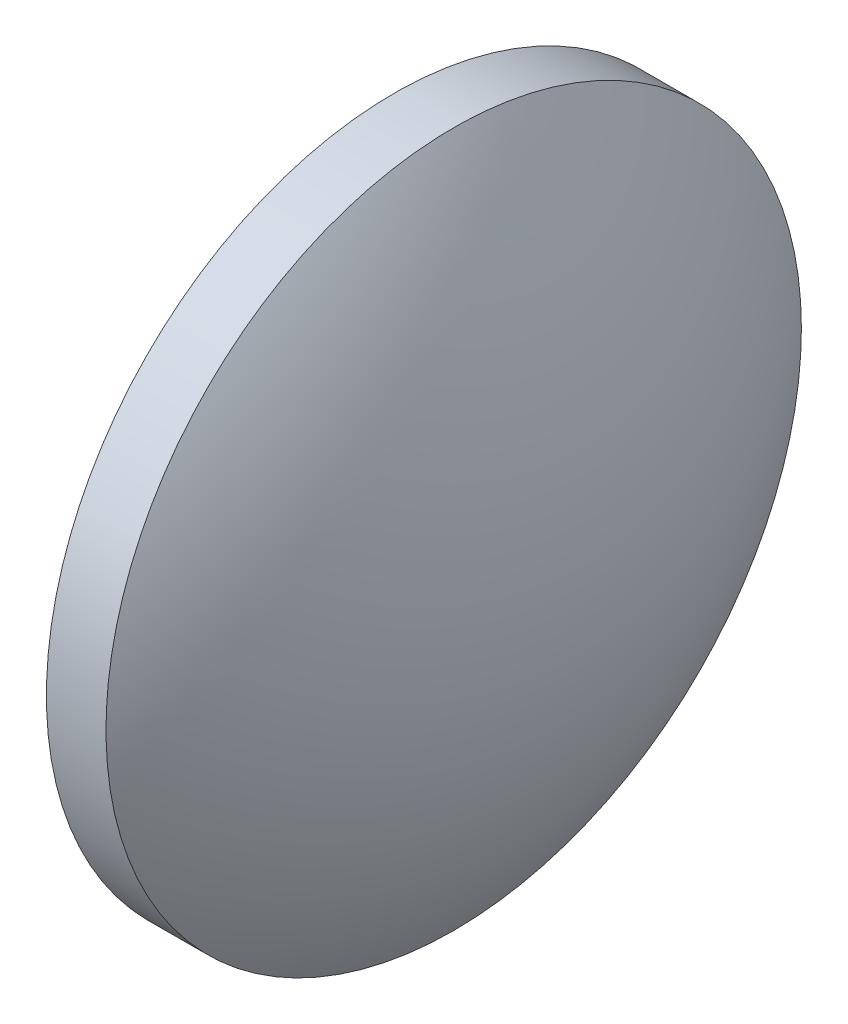
SolidWorks part; units mm, degrees
ref_plane "前视基准面" through (0, 0, 0) normal (0, 0, 1) x (1, 0, 0)
ref_plane "上视基准面" through (0, 0, 0) normal (0, 1, 0) x (1, 0, 0)
ref_plane "右视基准面" through (0, 0, 0) normal (1, 0, 0) x (0, 0, -1)
sketch "草图1" plane through (0, 0, 0) normal (0, 0, 1) x (1, 0, 0)
  line L0 (110.1654, 65.2336) -> (128.9614, 65.2336) construction
  line L1 (115.7736, 65.2336) -> (115.7736, 77.9336)
  line L2 (115.7736, 77.9336) -> (117.9494, 77.9336)
  line L3 (121.7736, 65.2336) -> (115.7736, 65.2336)
  arc A0 (121.7736, 65.2336) -> (117.9494, 77.9336) centre (98.7736, 65.2336) ccw
  dimension "D1" = 23
  dimension "D2" = 6
revolve "旋转1" add sketch "草图1" angle 360 about L3
